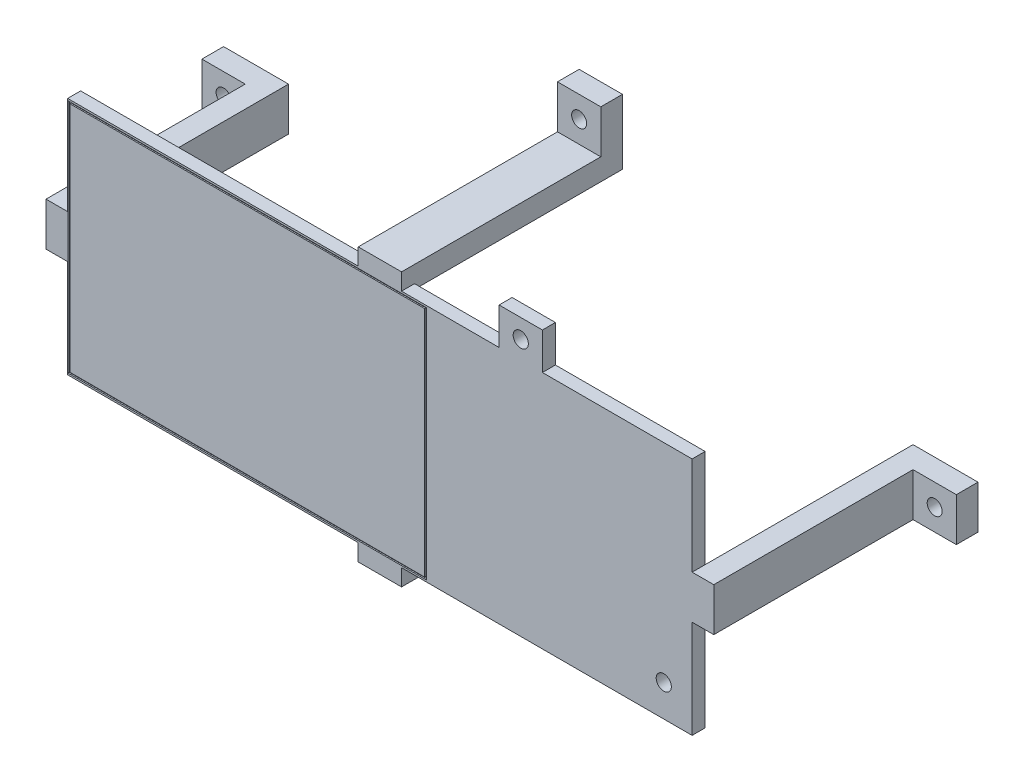
SolidWorks part; units mm, degrees
ref_plane "Front Plane" through (0, 0, 0) normal (0, 0, 1) x (1, 0, 0)
ref_plane "Top Plane" through (0, 0, 0) normal (0, 1, 0) x (1, 0, 0)
ref_plane "Right Plane" through (0, 0, 0) normal (1, 0, 0) x (0, 0, -1)
sketch "Sketch2" plane through (0, 0, 0) normal (0, 0, 1) x (1, 0, 0)
  line L0 (-68.085, -22.5) -> (68.085, 22.5) construction
  line L1 (-68.085, 22.5) -> (68.085, 22.5) construction
  line L2 (-68.085, 22.5) -> (-68.085, -22.5) construction
  line L3 (-68.085, -22.5) -> (68.085, -22.5) construction
  line L4 (68.085, 22.5) -> (68.085, -22.5) construction
  line L5 (-72.085, 26.5) -> (72.085, 26.5) construction
  line L6 (72.085, 26.5) -> (72.085, -26.5) construction
  line L7 (-72.085, -26.5) -> (72.085, -26.5) construction
  line L8 (-72.085, 26.5) -> (-72.085, -26.5) construction
  line L9 (0, 0) -> (-100, 0) construction
  line L10 (-77.085, 5) -> (-72.085, 5)
  line L11 (-77.085, 5) -> (-77.085, -5)
  line L12 (-77.085, -5) -> (-72.085, -5)
  line L13 (-72.085, 5) -> (-72.085, -5)
  line L14 (-5, 31.5) -> (5, 31.5)
  line L15 (-5, 31.5) -> (-5, 26.5)
  line L16 (-5, 26.5) -> (5, 26.5)
  line L17 (5, 31.5) -> (5, 26.5)
  line L18 (0, 0) -> (0, 108.7377) construction
  line L19 (-77.085, 5) -> (-72.085, -5) construction
  line L20 (-5, 26.5) -> (5, 31.5) construction
  line L21 (77.085, -5) -> (72.085, -5)
  line L22 (77.085, 5) -> (77.085, -5)
  line L23 (72.085, 5) -> (72.085, -5)
  line L24 (77.085, 5) -> (72.085, 5)
  line L25 (-5, -26.5) -> (5, -26.5)
  line L26 (-5, -31.5) -> (-5, -26.5)
  line L27 (-5, -31.5) -> (5, -31.5)
  line L28 (5, -31.5) -> (5, -26.5)
  point P4 (0, 0)
  point P23 (-74.585, 0)
  point P25 (0, 29)
  dimension "D1" = 45
  dimension "D2" = 136.17
  dimension "D4" = 5
  dimension "D5" = 10
  dimension "D6" = 5
  dimension "D7" = 10
  dimension "D3" = 4
extrude "Boss-Extrude1" add sketch "Sketch2" along normal blind 48
sketch "Sketch3" plane through (0, 0, 48) normal (0, 0, 1) x (1, 0, 0)
  line L0 (-82.5, 27.64) -> (82.5, -27.64) construction
  line L1 (-82.5, 27.64) -> (82.5, 27.64)
  line L2 (-82.5, 27.64) -> (-82.5, -27.64)
  line L3 (-82.5, -27.64) -> (82.5, -27.64)
  line L4 (82.5, 27.64) -> (82.5, -27.64)
  point P4 (0, 0)
  dimension "D1" = 165
  dimension "D2" = 55.28
extrude "Boss-Extrude2" add sketch "Sketch3" along normal blind 3
sketch "Sketch4" plane through (0, 0, 48) normal (0, 0, 1) x (1, 0, 0)
  line L0 (-5, 27.64) -> (5, 27.64) construction
  line L1 (5, 27.64) -> (5, 31.5) construction
  line L2 (5, 31.5) -> (-5, 31.5) construction
  line L3 (-5, 31.5) -> (-5, 27.64) construction
  line L4 (5, -31.5) -> (5, -27.64) construction
  line L5 (5, -27.64) -> (-5, -27.64) construction
  line L6 (-5, -27.64) -> (-5, -31.5) construction
  line L7 (-5, -31.5) -> (5, -31.5) construction
  line L8 (-5, 27.64) -> (5, 27.64)
  line L9 (5, 27.64) -> (5, 31.5)
  line L10 (5, 31.5) -> (-5, 31.5)
  line L11 (-5, 31.5) -> (-5, 27.64)
  line L12 (5, -31.5) -> (5, -27.64)
  line L13 (5, -27.64) -> (-5, -27.64)
  line L14 (-5, -27.64) -> (-5, -31.5)
  line L15 (-5, -31.5) -> (5, -31.5)
extrude "Boss-Extrude3" add sketch "Sketch4" along normal up to surface (3 mm away) up to face at (0, 0, 51)
sketch "Sketch5" plane through (0, 5, 0) normal (0, 1, 0) x (1, 0, 0)
  line L0 (0, 0) -> (0, -40.7206) construction
  line L1 (-77.085, 0) -> (-87.085, 0)
  line L2 (-77.085, 0) -> (-77.085, -5)
  line L3 (-77.085, -5) -> (-87.085, -5)
  line L4 (-87.085, 0) -> (-87.085, -5)
  line L5 (87.085, 0) -> (87.085, -5)
  line L6 (77.085, 0) -> (87.085, 0)
  line L7 (77.085, 0) -> (77.085, -5)
  line L8 (77.085, -5) -> (87.085, -5)
  dimension "D1" = 5
  dimension "D2" = 10
extrude "Boss-Extrude4" add sketch "Sketch5" against normal up to surface (10 mm away) up to face at (-74.585, -5, 24)
sketch "Sketch7" plane through (-5, 0, 0) normal (-1, 0, 0) x (0, 0, 1)
  line L0 (0, 0) -> (45.7182, 0) construction
  line L1 (0, 31.5) -> (5, 31.5)
  line L2 (0, 31.5) -> (0, 41.5)
  line L3 (0, 41.5) -> (5, 41.5)
  line L4 (5, 31.5) -> (5, 41.5)
  line L5 (0, -41.5) -> (5, -41.5)
  line L6 (0, -31.5) -> (0, -41.5)
  line L7 (0, -31.5) -> (5, -31.5)
  line L8 (5, -31.5) -> (5, -41.5)
  dimension "D1" = 5
  dimension "D2" = 10
extrude "Boss-Extrude5" add sketch "Sketch7" against normal up to surface (10 mm away) up to face at (5, -28.5467, 33)
sketch "Sketch8" plane through (0, 0, 5) normal (0, 0, 1) x (1, 0, 0)
  line L0 (-87.085, 5) -> (-77.085, -5) construction
  line L1 (-5, -31.5) -> (5, -41.5) construction
  line L2 (0, 0) -> (0, 49.5906) construction
  line L3 (0, 0) -> (57.6811, 0) construction
  circle A0 centre (-82.085, 0) radius 1.73
  circle A1 centre (0, -36.5) radius 1.73
  circle A2 centre (82.085, 0) radius 1.73
  circle A3 centre (0, 36.5) radius 1.73
  dimension "D1" = 3.46
  dimension "D2" = 3.46
extrude "Cut-Extrude1" cut sketch "Sketch8" against normal through all
sketch "Metro Express Layout Reference" plane through (0, 0, 51) normal (0, 0, 1) x (1, 0, 0)
  line L0 (0.32, 27.64) -> (0.32, -27.64) construction
  line L1 (14.74, 34.29) -> (68.08, 34.29) construction
  line L2 (14.74, 34.29) -> (14.74, -34.29) construction
  line L3 (14.74, -34.29) -> (68.08, -34.29) construction
  line L4 (68.08, 34.29) -> (68.08, -34.29) construction
  line L5 (82.5, -27.64) -> (82.5, 27.64) construction
  line L7 (-5, 27.64) -> (-82.5, 27.64) construction
  line L8 (-82.5, -27.64) -> (-5, -27.64) construction
  line L9 (-82.5, 27.64) -> (-82.5, -27.64) construction
  circle A0 centre (32.52, 31.75) radius 1.75 construction
  circle A1 centre (65.54, -20.32) radius 1.75 construction
  point P4 (68.08, 0)
  point P7 (82.5, 0)
  dimension "D5" = 3.5
  dimension "D7" = 3.5
  dimension "D1" = 68.58
  dimension "D2" = 53.34
  dimension "D3" = 17.78
  dimension "D4" = 2.54
  dimension "D6" = 13.97
  dimension "D8" = 2.54
  dimension "D9" = 82.82
  dimension "D10" = 14.42
sketch "Sketch10" plane through (0, 0, 51) normal (0, 0, 1) x (1, 0, 0)
  line L0 (82.5, 27.64) -> (5, 27.64) construction
  line L1 (27.52, 27.64) -> (37.52, 27.64)
  line L2 (27.52, 27.64) -> (27.52, 36.14)
  line L3 (27.52, 36.14) -> (37.52, 36.14)
  line L4 (37.52, 27.64) -> (37.52, 36.14)
  line L5 (68.08, 34.29) -> (68.08, -34.29) construction
  line L6 (68.08, -15.32) -> (69.93, -15.32)
  line L7 (68.08, -15.32) -> (68.08, -25.32)
  line L8 (68.08, -25.32) -> (69.93, -25.32)
  line L9 (69.93, -15.32) -> (69.93, -25.32)
  point P6 (32.52, 27.64)
  point P14 (68.08, -20.32)
  dimension "D1" = 8.5
  dimension "D2" = 10
  dimension "D3" = 10
  dimension "D4" = 4.39
extrude "Boss-Extrude6" add sketch "Sketch10" against normal up to surface (3 mm away) up to face at (74.585, 0, 48)
sketch "Sketch11" plane through (0, 0, 51) normal (0, 0, 1) x (1, 0, 0)
  circle A0 centre (32.52, 31.75) radius 1.75
  circle A1 centre (65.54, -20.32) radius 1.75
  circle A2 centre (32.52, 31.75) radius 1.75 construction
  circle A3 centre (65.54, -20.32) radius 1.75 construction
extrude "Cut-Extrude3" cut sketch "Sketch11" against normal through all
sketch "Sketch12" plane through (0, 0, 51) normal (0, 0, 1) x (1, 0, 0)
  line L0 (-82.5, 27.64) -> (-82.5, -27.64) construction
  line L1 (-71.785, 27.03) -> (10.535, 27.03) construction
  line L2 (-71.785, 27.03) -> (-71.785, -27.03) construction
  line L3 (-71.785, -27.03) -> (10.535, -27.03) construction
  line L4 (10.535, 27.03) -> (10.535, -27.03) construction
  line L5 (-71.985, 27.23) -> (-71.985, -27.23)
  line L6 (-12.815, 8.88) -> (12.815, 8.88) construction
  line L7 (-12.815, 8.88) -> (-12.815, -8.88) construction
  line L8 (-12.815, -8.88) -> (12.815, -8.88) construction
  line L9 (12.815, 8.88) -> (12.815, -8.88) construction
  line L10 (-71.985, -27.23) -> (10.735, -27.23)
  line L11 (10.735, 27.23) -> (10.735, -27.23)
  line L12 (-71.985, 27.23) -> (10.735, 27.23)
  line L13 (-71.585, 26.83) -> (-71.585, -26.83)
  line L14 (-71.585, -26.83) -> (10.335, -26.83)
  line L15 (10.335, 26.83) -> (10.335, -26.83)
  line L16 (-71.585, 26.83) -> (10.335, 26.83)
  point P4 (12.815, 0)
  point P5 (-71.785, 0)
  point P8 (-82.5, 0)
  point P15 (0, 8.88)
  dimension "D1" = 82.32
  dimension "D2" = 54.06
  dimension "D3" = 25.63
  dimension "D4" = 17.76
  dimension "D5" = 2.28
  dimension "D6" = 0.2
  dimension "D7" = 0.2
extrude "Cut-Extrude4" cut sketch "Sketch12" against normal blind 0.28
sketch "Sketch13" plane through (0, 0, 48) normal (0, 0, -1) x (-1, 0, 0)
  line L0 (82.5, -27.64) -> (82.5, 27.64)
  line L5 (-82.5, 27.64) -> (-82.5, -27.64)
  line L17 (-82.5, 27.64) -> (-37.52, 27.64) construction
  line L18 (-82.5, -27.64) -> (-72.085, -27.64)
  line L20 (-77.085, -5) -> (-72.085, -5)
  line L21 (-72.085, -27.64) -> (-72.085, -5)
  line L25 (-77.085, -5) -> (-77.085, 5)
  line L26 (-77.085, 5) -> (-72.085, 5)
  line L28 (-82.5, 27.64) -> (-72.085, 27.64)
  line L29 (-72.085, 5) -> (-72.085, 27.64)
  line L30 (5, 27.64) -> (82.5, 27.64) construction
  line L31 (82.5, -27.64) -> (72.085, -27.64)
  line L33 (77.085, -5) -> (72.085, -5)
  line L34 (72.085, -27.64) -> (72.085, -5)
  line L38 (77.085, -5) -> (77.085, 5)
  line L39 (77.085, 5) -> (72.085, 5)
  line L41 (82.5, 27.64) -> (72.085, 27.64)
  line L42 (72.085, 5) -> (72.085, 27.64)
extrude "Cut-Extrude5" cut sketch "Sketch13" against normal through all
